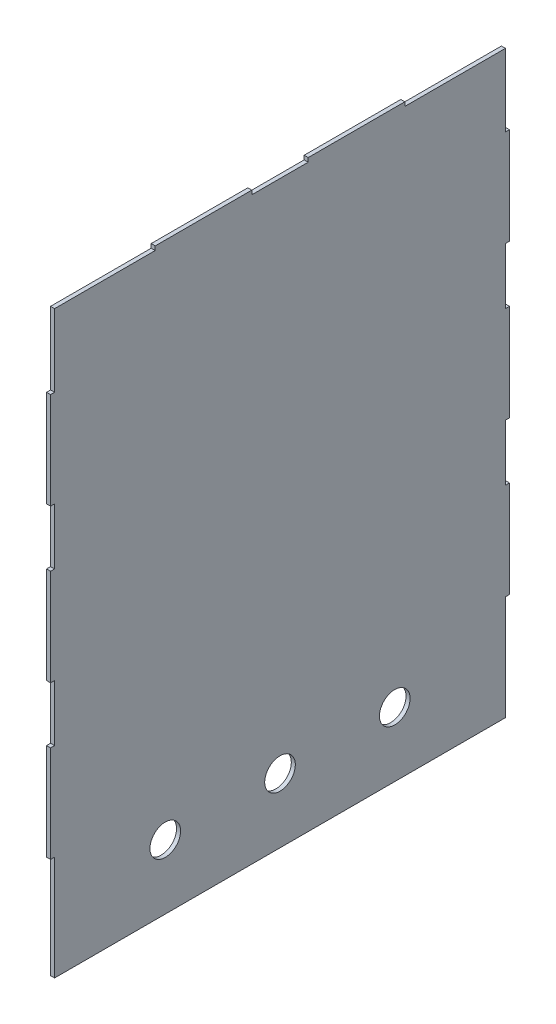
SolidWorks part; units mm, degrees
ref_plane "Front Plane" through (0, 0, 0) normal (0, 0, 1) x (1, 0, 0)
ref_plane "Top Plane" through (0, 0, 0) normal (0, 1, 0) x (1, 0, 0)
ref_plane "Right Plane" through (0, 0, 0) normal (1, 0, 0) x (0, 0, -1)
sketch "Sketch1" plane through (0, 0, 0) normal (1, 0, 0) x (0, 0, -1)
  line L1 (-180.975, 0) -> (180.975, 0)
  line L2 (-180.975, 0) -> (-180.975, 460.375)
  line L3 (-180.975, 460.375) -> (180.975, 460.375)
  line L4 (180.975, 0) -> (180.975, 460.375)
  point P4 (0, 0)
  dimension "D1" = 361.95
  dimension "D2" = 460.375
extrude "Boss-Extrude1" add sketch "Sketch1" along normal blind 3.175
sketch "Sketch2" plane through (3.175, 0, 0) normal (1, 0, 0) x (0, 0, -1)
  line L0 (-180.975, 460.375) -> (-98.425, 460.375)
  line L1 (180.975, 460.375) -> (-180.975, 460.375) construction
  line L2 (-98.425, 460.375) -> (-98.425, 457.2)
  line L3 (-98.425, 457.2) -> (-177.8, 457.2)
  line L4 (-177.8, 457.2) -> (-177.8, 400.05)
  line L5 (-177.8, 400.05) -> (-180.975, 400.05)
  line L6 (-180.975, 460.375) -> (-180.975, 0) construction
  line L7 (-180.975, 400.05) -> (-180.975, 460.375)
  line L8 (-180.975, 82.55) -> (-180.975, 0)
  line L9 (-180.975, 0) -> (-177.8, 0)
  line L10 (-180.975, 0) -> (180.975, 0) construction
  line L11 (-177.8, 0) -> (-177.8, 82.55)
  line L12 (-177.8, 82.55) -> (-180.975, 82.55)
  line L13 (-180.975, 158.75) -> (-177.8, 158.75)
  line L14 (-177.8, 158.75) -> (-177.8, 203.2)
  line L15 (-177.8, 203.2) -> (-180.975, 203.2)
  line L16 (-180.975, 203.2) -> (-180.975, 158.75)
  line L17 (-180.975, 279.4) -> (-177.8, 279.4)
  line L18 (-177.8, 279.4) -> (-177.8, 323.85)
  line L19 (-177.8, 323.85) -> (-180.975, 323.85)
  line L20 (-180.975, 323.85) -> (-180.975, 279.4)
  line L21 (-22.225, 460.375) -> (-22.225, 457.2)
  line L22 (-22.225, 457.2) -> (22.225, 457.2)
  line L23 (0, 457.2) -> (0, 460.375)
  line L24 (22.225, 460.375) -> (-22.225, 460.375)
  line L25 (0, -9.8078) -> (0, 519.6894) construction
  line L26 (22.225, 460.375) -> (22.225, 457.2)
  line L27 (180.975, 323.85) -> (180.975, 279.4)
  line L28 (177.8, 323.85) -> (180.975, 323.85)
  line L29 (177.8, 279.4) -> (177.8, 323.85)
  line L30 (180.975, 279.4) -> (177.8, 279.4)
  line L31 (180.975, 203.2) -> (180.975, 158.75)
  line L32 (177.8, 203.2) -> (180.975, 203.2)
  line L33 (177.8, 158.75) -> (177.8, 203.2)
  line L34 (180.975, 158.75) -> (177.8, 158.75)
  line L35 (177.8, 82.55) -> (180.975, 82.55)
  line L36 (177.8, 0) -> (177.8, 82.55)
  line L37 (180.975, 0) -> (177.8, 0)
  line L38 (180.975, 82.55) -> (180.975, 0)
  line L39 (180.975, 400.05) -> (180.975, 460.375)
  line L40 (177.8, 400.05) -> (180.975, 400.05)
  line L41 (177.8, 457.2) -> (177.8, 400.05)
  line L42 (98.425, 457.2) -> (177.8, 457.2)
  line L43 (98.425, 460.375) -> (98.425, 457.2)
  line L44 (180.975, 460.375) -> (98.425, 460.375)
  line M2 (-180.975, 460.375) -> (-180.975, 0)
  line M3 (-180.975, 0) -> (180.975, 0)
  line M4 (180.975, 0) -> (180.975, 460.375)
  line M5 (180.975, 460.375) -> (-180.975, 460.375)
  dimension "D1" = 76.2
  dimension "D2" = 76.2
  dimension "D3" = 76.2
  dimension "D4" = 3.175
  dimension "D5" = 3.175
  dimension "D6" = 3.175
  dimension "D7" = 3.175
  dimension "D8" = 3.175
  dimension "D9" = 3.175
  dimension "D10" = 82.55
  dimension "D11" = 76.2
  dimension "D12" = 60.325
  dimension "D13" = 44.45
  dimension "D14" = 44.45
extrude "Cut-Extrude1" cut sketch "Sketch2" against normal blind 3.175 contours L11 L12 M2 M3 | L14 L15 L13 M2 | L18 L19 L17 M2 | L5 L4 L3 L2 M5 M2 | L22 L23 L21 M5 | L26 L23 L22 M5 | L43 L42 L41 L40 M5 M4 | L30 L28 L29 M4 | L34 L32 L33 M4 | L36 L35 M3 M4
sketch "Sketch3" plane through (3.175, 0, 0) normal (1, 0, 0) x (0, 0, -1)
  line L0 (-177.8, 0) -> (177.8, 0) construction
  circle A0 centre (0, 50.8) radius 12.0777
  circle A1 centre (-90.5002, 50.8) radius 12.0777
  circle A2 centre (90.5002, 50.8) radius 12.0777
  dimension "D1" = 24.1554
  dimension "D2" = 24.1554
  dimension "D3" = 24.1554
  dimension "D4" = 90.5002
  dimension "D5" = 90.5002
  dimension "D6" = 50.8
extrude "Cut-Extrude2" cut sketch "Sketch3" against normal blind 3.175
